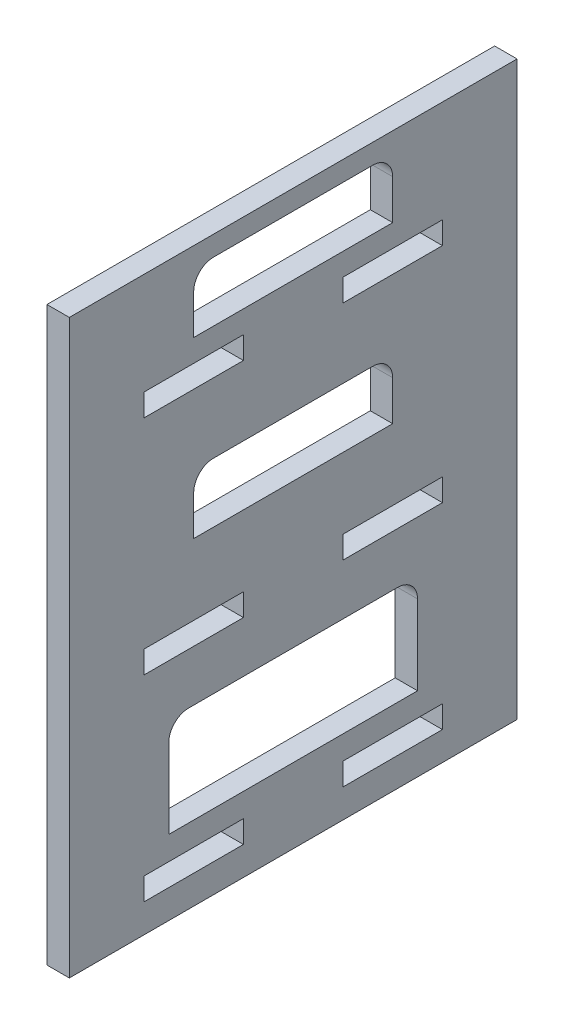
SolidWorks part; units mm, degrees
ref_plane "Front Plane" through (0, 0, 0) normal (0, 0, 1) x (1, 0, 0)
ref_plane "Top Plane" through (0, 0, 0) normal (0, 1, 0) x (1, 0, 0)
ref_plane "Right Plane" through (0, 0, 0) normal (1, 0, 0) x (0, 0, -1)
sketch "Sketch1" plane through (0, 0, 0) normal (1, 0, 0) x (0, 0, -1)
  line L0 (0, 0) -> (0, 5)
  line L1 (0, 5) -> (0, 45)
  line L3 (90, 5) -> (90, 45)
  line L4 (0, 45) -> (0, 50)
  line L5 (0, 50) -> (0, 90)
  line L6 (0, 90) -> (0, 95)
  line L7 (0, 95) -> (0, 115)
  line L8 (0, 115) -> (90, 115)
  line L9 (90, 115) -> (90, 45)
  line L10 (45, 115) -> (45, 105)
  line L11 (0, 0) -> (90, 0)
  line L12 (25, 111) -> (65, 111)
  line L13 (25, 111) -> (25, 99)
  line L14 (25, 99) -> (65, 99)
  line L15 (65, 111) -> (65, 99)
  line L16 (25, 111) -> (65, 99) construction
  line L17 (25, 99) -> (65, 111) construction
  line L18 (90, 0) -> (90, 5)
  line L19 (45, 70) -> (45, 115)
  line L20 (45, 115) -> (45, 25)
  line L21 (25, 76) -> (65, 76)
  line L22 (25, 76) -> (25, 64)
  line L23 (25, 64) -> (65, 64)
  line L24 (65, 76) -> (65, 64)
  line L25 (25, 76) -> (65, 64) construction
  line L26 (25, 64) -> (65, 76) construction
  line L27 (0, 92.25) -> (25, 92.25)
  line L28 (20, 35) -> (70, 35)
  line L29 (20, 35) -> (20, 15)
  line L30 (20, 15) -> (70, 15)
  line L31 (70, 35) -> (70, 15)
  line L32 (20, 35) -> (70, 15) construction
  line L33 (20, 15) -> (70, 35) construction
  line L34 (55, 94.5) -> (55, 90)
  line L35 (75, 94.5) -> (75, 90)
  line L36 (15, 94.5) -> (35, 94.5)
  line L37 (15, 94.5) -> (15, 90)
  line L38 (15, 90) -> (35, 90)
  line L39 (35, 94.5) -> (35, 90)
  line L40 (15, 94.5) -> (35, 90) construction
  line L41 (15, 90) -> (35, 94.5) construction
  line L42 (75, 94.5) -> (55, 94.5)
  line L43 (75, 90) -> (55, 90)
  line L44 (0, 47.5) -> (25, 47.5)
  line L45 (75, 45.25) -> (55, 45.25)
  line L46 (15, 49.75) -> (35, 49.75)
  line L47 (15, 49.75) -> (15, 45.25)
  line L48 (15, 45.25) -> (35, 45.25)
  line L49 (35, 49.75) -> (35, 45.25)
  line L50 (15, 49.75) -> (35, 45.25) construction
  line L51 (15, 45.25) -> (35, 49.75) construction
  line L52 (55, 49.75) -> (55, 45.25)
  line L53 (75, 49.75) -> (55, 49.75)
  line L54 (75, 49.75) -> (75, 45.25)
  line L55 (25, 0) -> (25, 8)
  line L56 (55, 10.25) -> (55, 5.75)
  line L57 (15, 10.25) -> (35, 10.25)
  line L58 (15, 10.25) -> (15, 5.75)
  line L59 (15, 5.75) -> (35, 5.75)
  line L60 (35, 10.25) -> (35, 5.75)
  line L61 (15, 10.25) -> (35, 5.75) construction
  line L62 (15, 5.75) -> (35, 10.25) construction
  line L63 (75, 10.25) -> (75, 5.75)
  line L64 (75, 5.75) -> (55, 5.75)
  line L65 (75, 10.25) -> (55, 10.25)
  dimension "D1" = 5
  dimension "D2" = 40
  dimension "D3" = 90
  dimension "D4" = 40
  dimension "D5" = 5
  dimension "D6" = 5
  dimension "40" = 40
  dimension "D7" = 20
  dimension "D8" = 12
  dimension "D9" = 40
  dimension "D10" = 45
  dimension "D11" = 40
  dimension "D12" = 12
  dimension "D13" = 90
  dimension "D14" = 20
  dimension "D15" = 50
  dimension "D16" = 4.5
  dimension "D17" = 20
  dimension "D18" = 20
  dimension "D19" = 4.5
  dimension "D20" = 20
  dimension "D21" = 4.5
  dimension "D22" = 8
extrude "Boss-Extrude1" add sketch "Sketch1" along normal blind 4.5
fillet "Fillet1" radius 4 6 edges at (2.25, 35, -20) (2.25, 35, -70) (2.25, 76, -25) (2.25, 76, -65) (2.25, 111, -25) (2.25, 111, -65)
